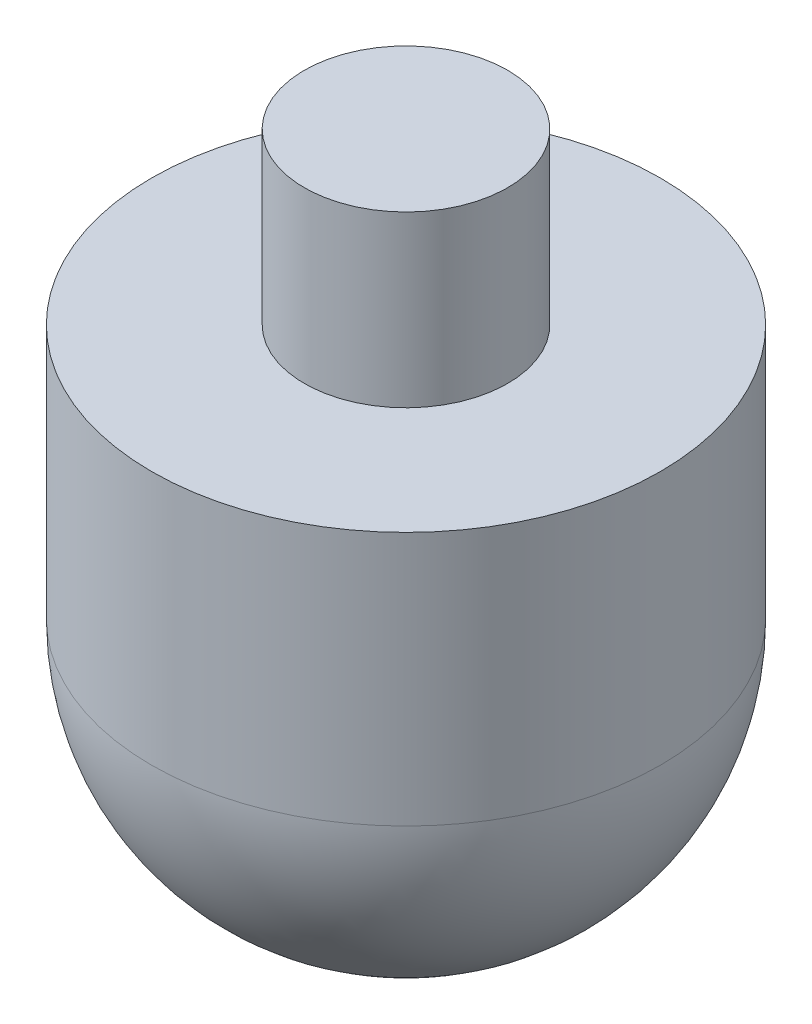
SolidWorks part; units mm, degrees
ref_plane "Front Plane" through (0, 0, 0) normal (0, 0, 1) x (1, 0, 0)
ref_plane "Top Plane" through (0, 0, 0) normal (0, 1, 0) x (1, 0, 0)
ref_plane "Right Plane" through (0, 0, 0) normal (1, 0, 0) x (0, 0, -1)
sketch "Sketch1" plane through (0, 0, 0) normal (0, 0, 1) x (1, 0, 0)
  line L0 (0, 0) -> (0, 43.8525) construction
  line L1 (0, 0) -> (6, 0)
  line L2 (6, 0) -> (6, -10)
  line L3 (6, -10) -> (15, -10)
  line L4 (15, -10) -> (15, -25)
  line L5 (0, 0) -> (0, -40)
  arc A0 (15, -25) -> (0, -40) centre (0, -25) cw
  dimension "D1" = 30
  dimension "D2" = 12
  dimension "D3" = 10
  dimension "D4" = 15
revolve "Revolve1" add sketch "Sketch1" angle 360 about L0
